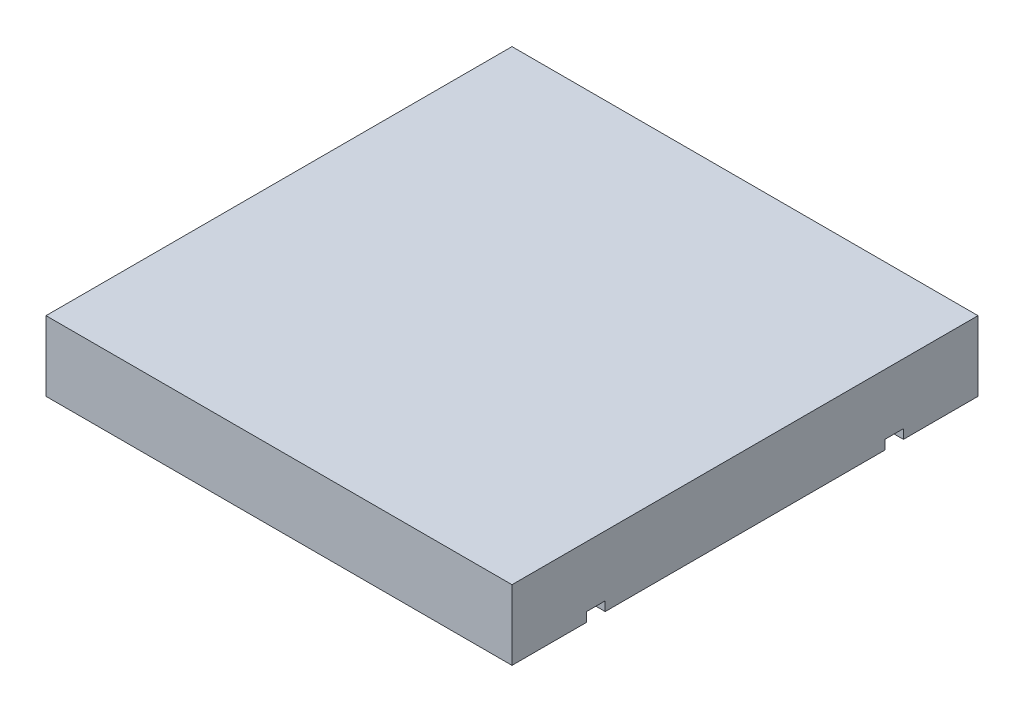
SolidWorks part; units mm, degrees
ref_plane "Plano frontal" through (0, 0, 0) normal (0, 0, 1) x (1, 0, 0)
ref_plane "Plano superior" through (0, 0, 0) normal (0, 1, 0) x (1, 0, 0)
ref_plane "Plano direito" through (0, 0, 0) normal (1, 0, 0) x (0, 0, -1)
sketch "Esboço1" plane through (0, 0, 0) normal (0, 1, 0) x (1, 0, 0)
  line L1 (-500, -500) -> (500, -500)
  line L2 (-500, -500) -> (-500, 500)
  line L3 (-500, 500) -> (500, 500)
  line L4 (500, -500) -> (500, 500)
  line L5 (-500, -500) -> (500, 500) construction
  line L6 (-500, 500) -> (500, -500) construction
  point P0 (0, 0)
  dimension "D1" = 1000
extrude "Ressalto-extrusão1" add sketch "Esboço1" along normal blind 150
sketch "Esboço2" plane through (-500, 0, 0) normal (-1, 0, 0) x (0, 0, 1)
  line L0 (-500, 0) -> (500, 0) construction
  line L1 (300, -20) -> (340, -20)
  line L2 (300, -20) -> (300, 20)
  line L3 (300, 20) -> (340, 20)
  line L4 (340, -20) -> (340, 20)
  line L5 (300, -20) -> (340, 20) construction
  line L6 (300, 20) -> (340, -20) construction
  line L7 (0, 0) -> (0, 479.2) construction
  line L8 (-300, 20) -> (-340, -20) construction
  line L9 (-300, -20) -> (-340, 20) construction
  line L10 (-340, -20) -> (-340, 20)
  line L11 (-300, 20) -> (-340, 20)
  line L12 (-300, -20) -> (-300, 20)
  line L13 (-300, -20) -> (-340, -20)
  point P0 (320, 0)
  point P14 (-320, 0)
  dimension "D1" = 40
  dimension "D2" = 600
extrude "Corte-extrusão1" cut sketch "Esboço2" against normal through all
